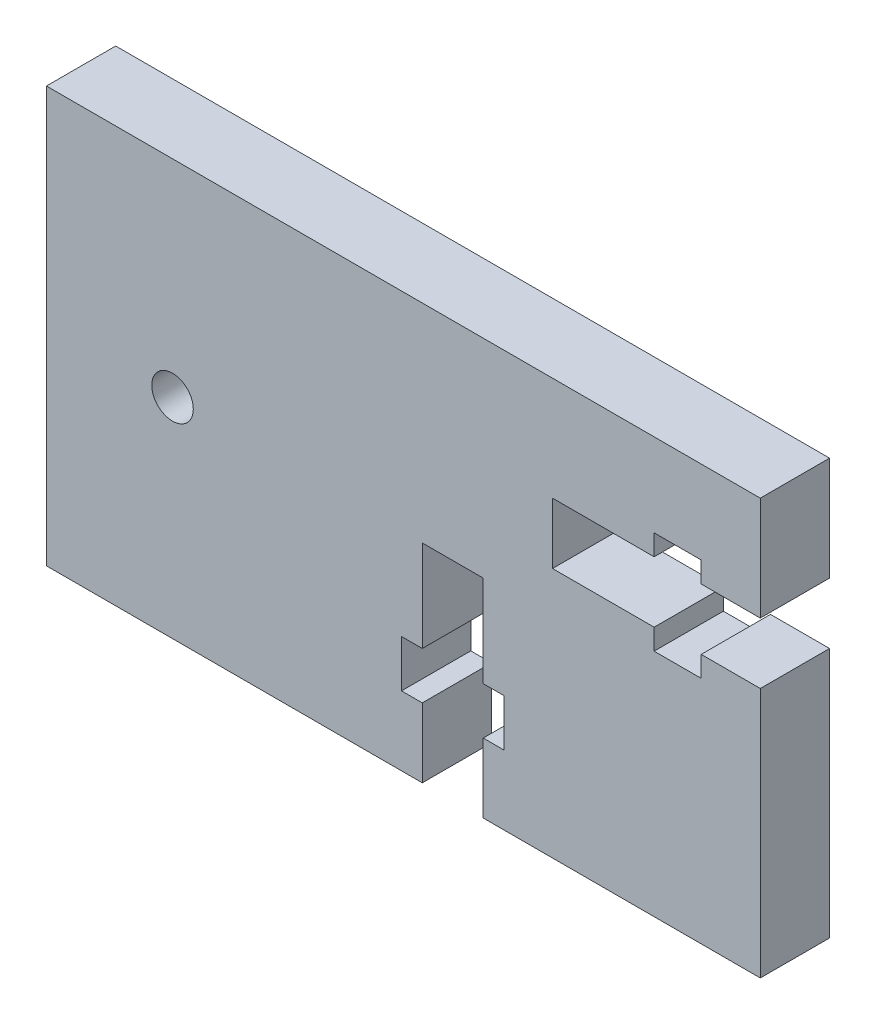
SolidWorks part; units mm, degrees
ref_plane "Front Plane" through (0, 0, 0) normal (0, 0, 1) x (1, 0, 0)
ref_plane "Top Plane" through (0, 0, 0) normal (0, 1, 0) x (1, 0, 0)
ref_plane "Right Plane" through (0, 0, 0) normal (1, 0, 0) x (0, 0, -1)
sketch "Sketch1" plane through (0, 0, 0) normal (0, 0, 1) x (1, 0, 0)
  line L1 (-23, 10) -> (28.53, 10)
  line L2 (-23, 10) -> (-23, -20)
  line L3 (-23, -20) -> (28.53, -20)
  line L4 (28.53, 10) -> (28.53, -20)
  dimension "D1" = 51.53
  dimension "30" = 30
  dimension "D3" = 23
  dimension "D4" = 10
extrude "Boss-Extrude1" add sketch "Sketch1" along normal blind 5
sketch "Sketch2" plane through (0, 0, 5) normal (0, 0, 1) x (1, 0, 0)
  line L0 (-23, -20) -> (28.53, -20) construction
  line L1 (13.53, -1.9) -> (20.8659, -1.9)
  line L2 (28.53, -1.9) -> (28.53, 2.5)
  line L3 (28.53, 2.5) -> (24.2659, 2.5)
  line L4 (13.53, -1.9) -> (13.53, 2.5)
  line L5 (20.8659, -1.9) -> (20.8659, -3.4)
  line L6 (20.8659, -3.4) -> (24.2659, -3.4)
  line L7 (24.2659, -3.4) -> (24.2659, -1.9)
  line L8 (20.8659, 2.5) -> (20.8659, 4)
  line L9 (20.8659, 4) -> (24.2659, 4)
  line L10 (24.2659, 4) -> (24.2659, 2.5)
  line L11 (24.2659, -1.9) -> (28.53, -1.9)
  line L12 (20.8659, 2.5) -> (13.53, 2.5)
  line L13 (28.53, -20) -> (28.53, 10) construction
  line L14 (28.53, 10) -> (-23, 10) construction
  line L15 (-2.6961, 5.9568) -> (-2.6961, -8.8884) construction
  line L16 (4.13, -5) -> (4.13, -11.6)
  line L17 (4.13, -20) -> (8.53, -20)
  line L18 (8.53, -20) -> (8.53, -15)
  line L19 (4.13, -5) -> (8.53, -5)
  line L20 (4.13, -11.6) -> (2.63, -11.6)
  line L21 (2.63, -11.6) -> (2.63, -15)
  line L22 (2.63, -15) -> (4.13, -15)
  line L23 (8.53, -11.6) -> (10.03, -11.6)
  line L24 (10.03, -11.6) -> (10.03, -15)
  line L25 (10.03, -15) -> (8.53, -15)
  line L26 (4.13, -15) -> (4.13, -20)
  line L27 (8.53, -11.6) -> (8.53, -5)
  dimension "D1" = 4.4
  dimension "D2" = 1.5
  dimension "D3" = 3.4
  dimension "D4" = 7.5
  dimension "D5" = 15
  dimension "D6" = 5
  dimension "D7" = 15
  dimension "D8" = 20
  dimension "D9" = 4.4
  dimension "D10" = 1.5
  dimension "D11" = 1.5
  dimension "D12" = 7.4
  dimension "D13" = 3.4
extrude "Cut-Extrude1" cut sketch "Sketch2" against normal blind 5
sketch "Sketch4" plane through (0, 0, 5) normal (0, 0, 1) x (1, 0, 0)
  line L0 (28.53, 10) -> (-23, 10) construction
  circle A1 centre (-13.8996, -4.9036) radius 1.5
  dimension "D3" = 3
  dimension "D1" = 14.9036
  dimension "D2" = 13.8996
extrude "Cut-Extrude3" cut sketch "Sketch4" against normal blind 5
